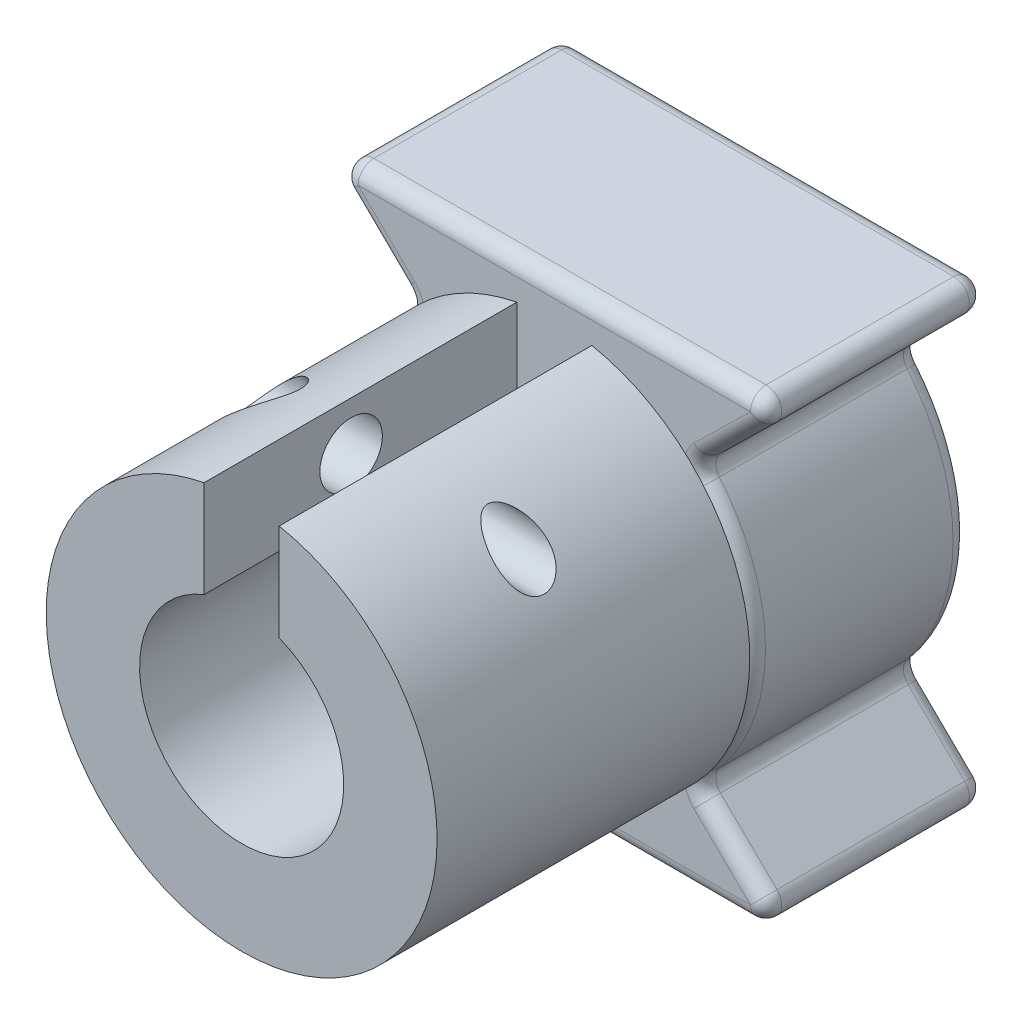
SolidWorks part; units mm, degrees
ref_plane "Front Plane" through (0, 0, 0) normal (0, 0, 1) x (1, 0, 0)
ref_plane "Top Plane" through (0, 0, 0) normal (0, 1, 0) x (1, 0, 0)
ref_plane "Right Plane" through (0, 0, 0) normal (1, 0, 0) x (0, 0, -1)
sketch "Sketch1" plane through (0, 0, 0) normal (0, 0, 1) x (1, 0, 0)
  circle A0 centre (0, 0) radius 6.25
  circle A1 centre (0, 0) radius 3.2639
  dimension "D1" = 12.5
  dimension "D2" = 6.5278
extrude "Boss-Extrude1" add sketch "Sketch1" along normal blind 10
sketch "Sketch2" plane through (0, 0, 0) normal (0, 0, -1) x (-1, 0, 0)
  line L0 (-7.5, 7.3314) -> (-4.4694, 4.3689) construction
  line L1 (-7.5, 7.3314) -> (7.5, 7.3314)
  line L2 (4.4694, -4.3689) -> (7.5, -7.3314) construction
  line L3 (-7.5, -7.3314) -> (7.5, -7.3314)
  line L4 (-2.334, 2.2815) -> (2.334, -2.2815) construction
  line L5 (-7.5, -7.3314) -> (-4.4694, -4.3689)
  line L7 (-4.4694, 4.3689) -> (-7.5, 7.3314)
  line L8 (7.5, -7.3314) -> (4.4694, -4.3689)
  line L10 (4.4694, 4.3689) -> (7.5, 7.3314)
  circle A0 centre (0, 0) radius 6.25 construction
  circle A1 centre (0, 0) radius 3.2639 construction
  circle A2 centre (0, 0) radius 3.2639
  arc A3 (4.4694, -4.3689) -> (4.4694, 4.3689) centre (0, 0) ccw
  arc A4 (-4.4694, 4.3689) -> (-4.4694, -4.3689) centre (0, 0) ccw
  dimension "D1" = 15
extrude "Boss-Extrude2" add sketch "Sketch2" along normal blind 7 separate body
sketch "Sketch3" plane through (0, 0, 10) normal (0, 0, 1) x (1, 0, 0)
  line L0 (0, 0) -> (0, 1.9522) construction
  line L1 (1.2, 7.1048) -> (-1.2, 7.1048)
  line L2 (1.2, 7.1048) -> (1.2, 1.9522)
  line L3 (1.2, 1.9522) -> (-1.2, 1.9522)
  line L4 (-1.2, 7.1048) -> (-1.2, 1.9522)
  dimension "D1" = 2.4
extrude "Cut-Extrude1" cut sketch "Sketch3" against normal blind 10
sketch "Sketch4" plane through (0, 0, 0) normal (1, 0, 0) x (0, 0, -1)
  line L0 (-10, 6.1337) -> (-10, 3.0353) construction
  line L1 (-10, 6.1337) -> (-10, 3.0353) construction
  line L2 (-10, 4.5845) -> (-5.3, 4.5845) construction
  line L3 (0, 6.1337) -> (0, 3.0353) construction
  circle A0 centre (-5.3, 4.5845) radius 1
  dimension "D2" = 2
  dimension "D1" = 5.3
extrude "Cut-Extrude2" cut sketch "Sketch4" against normal through all
sketch "Sketch5" plane through (0, 0, 0) normal (1, 0, 0) x (0, 0, -1)
  circle A0 centre (-5.3, 4.5845) radius 0.8
  circle A1 centre (-5.3, 4.5845) radius 1
  circle A2 centre (-5.3, 4.5845) radius 1 construction
  dimension "D2" = 1.6
  dimension "D1" = 0
extrude "m2x.4 thread" cut sketch "Sketch5" along normal blind 9.5
fillet "Fillet2" radius 0.5 24 edges at (5.9847, 5.8501, -7) (5.9847, 5.8501, 0) (5.9847, -5.8501, -7) (5.9847, -5.8501, 0) (-5.9847, -5.8501, -7) (-5.9847, -5.8501, 0) (-5.9847, 5.8501, -7) (-5.9847, 5.8501, 0) (4.4694, 4.3689, -3.5) (6.25, 0, -7) (4.4694, -4.3689, -3.5) (6.25, 0, 0) (-4.4694, -4.3689, -3.5) (-6.25, 0, -7) (-4.4694, 4.3689, -3.5) (-6.25, 0, 0) (-7.5, 7.3314, -3.5) (0, 7.3314, -7) (7.5, 7.3314, -3.5) (0, 7.3314, 0) (7.5, -7.3314, -3.5) (0, -7.3314, -7) (-7.5, -7.3314, -3.5) (0, -7.3314, 0)
